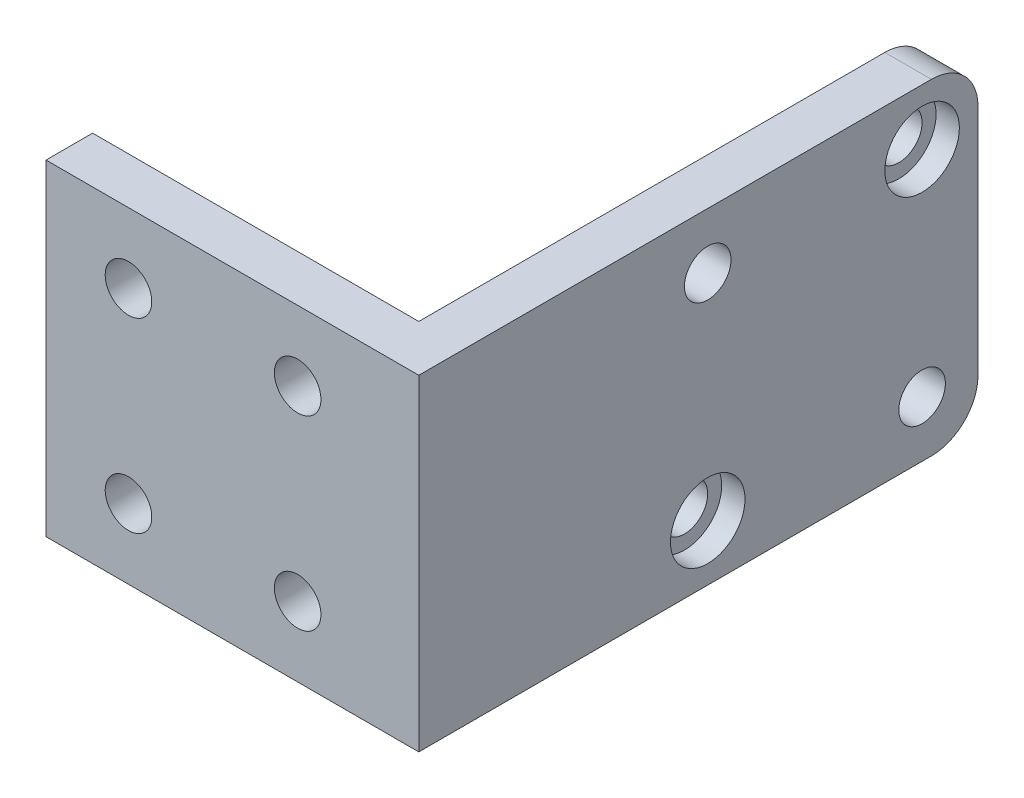
SolidWorks part; units mm, degrees
ref_plane "Front Plane" through (0, 0, 0) normal (0, 0, 1) x (1, 0, 0)
ref_plane "Top Plane" through (0, 0, 0) normal (0, 1, 0) x (1, 0, 0)
ref_plane "Right Plane" through (0, 0, 0) normal (1, 0, 0) x (0, 0, -1)
sketch "Sketch1" plane through (0, 0, 0) normal (0, 1, 0) x (1, 0, 0)
  line L0 (0, 0) -> (0, 5)
  line L1 (0, 5) -> (35, 5)
  line L2 (35, 5) -> (35, 60)
  line L3 (35, 60) -> (40, 60)
  line L4 (40, 60) -> (40, 0)
  line L5 (40, 0) -> (0, 0)
  dimension "D1" = 40
  dimension "D2" = 60
  dimension "D3" = 5
  dimension "D4" = 5
extrude "Boss-Extrude1" add sketch "Sketch1" along normal blind 35
fillet "Fillet1" radius 5 2 edges at (37.5, 0, -60) (37.5, 35, -60)
sketch "Sketch2" plane through (0, 0, -5) normal (0, 0, -1) x (-1, 0, 0)
  line L0 (-35, 35) -> (0, 35) construction
  line L1 (-35, 0) -> (0, 0) construction
  circle A0 centre (-27.0004, 27.5) radius 2.5
  circle A1 centre (-8.8512, 27.5) radius 2.5
  circle A2 centre (-27.0004, 7.5) radius 2.5
  circle A3 centre (-8.8512, 7.5) radius 2.5
  point P10 (0, 0)
  point P11 (0, 0)
  point P14 (0, 0)
  point P15 (0, 0)
  dimension "D1" = 5
  dimension "D2" = 7.5
  dimension "D3" = 7.5
extrude "Cut-Extrude1" cut sketch "Sketch2" against normal through all
sketch "Sketch3" plane through (35, 0, 0) normal (-1, 0, 0) x (0, 0, 1)
  line L0 (-60, 30) -> (-60, 5) construction
  line L1 (-55, 0) -> (-5, 0) construction
  line L2 (-55, 35) -> (-5, 35) construction
  circle A0 centre (-31, 29) radius 2.5
  circle A1 centre (-54, 6) radius 2.5
  circle A2 centre (-54, 29) radius 2.5
  circle A3 centre (-31, 6) radius 2.5
  point P14 (0, 0)
  dimension "D3" = 5
  dimension "D5" = 5
  dimension "D6" = 5
  dimension "D1" = 6
  dimension "D2" = 6
  dimension "D4" = 23
  dimension "D7" = 6
  dimension "D8" = 6
  dimension "D9" = 6
extrude "Cut-Extrude3" cut sketch "Sketch3" against normal through all contours A0 | A1 | A2 | A3
sketch "Sketch5" plane through (40, 0, 0) normal (1, 0, 0) x (0, 0, -1)
  circle A0 centre (54, 29) radius 4
  circle A1 centre (31, 6) radius 4
  dimension "D1" = 8
  dimension "D2" = 8
extrude "Cut-Extrude5" cut sketch "Sketch5" against normal blind 2.5
